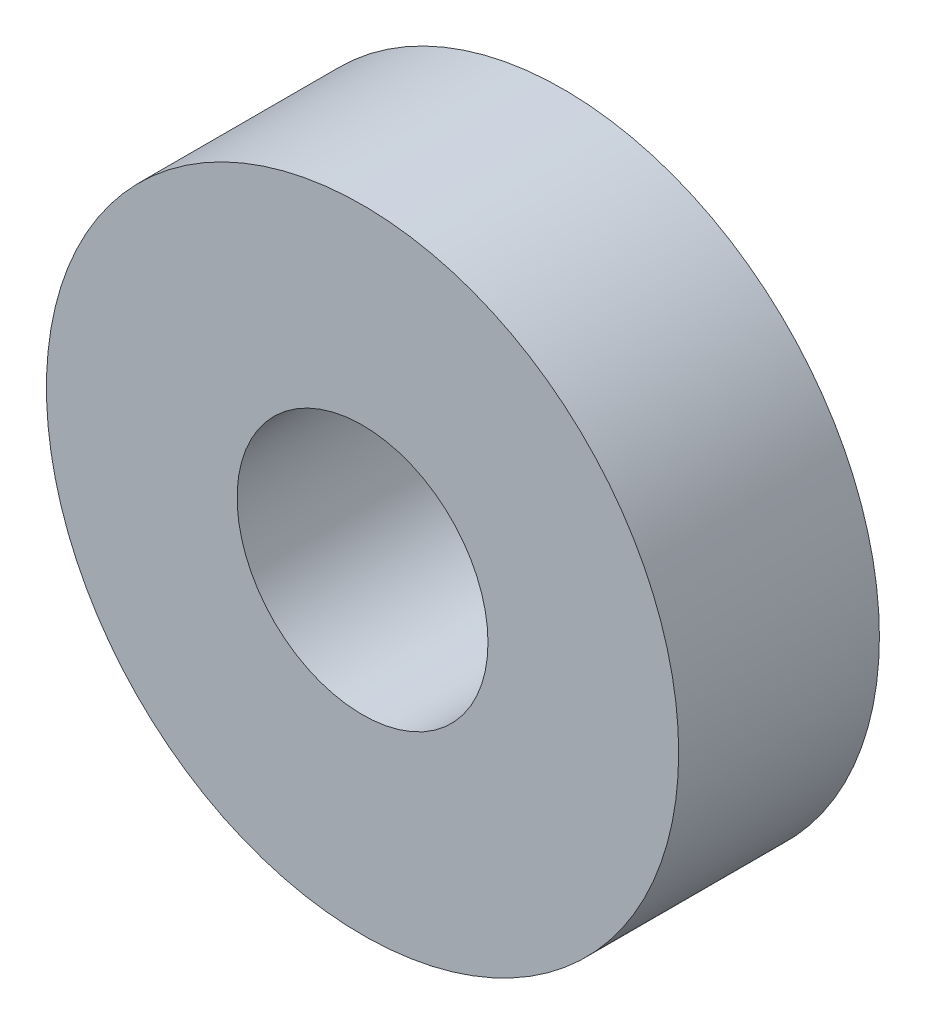
SolidWorks part; units mm, degrees
ref_plane "Plan de face" through (0, 0, 0) normal (0, 0, 1) x (1, 0, 0)
ref_plane "Plan de dessus" through (0, 0, 0) normal (0, 1, 0) x (1, 0, 0)
ref_plane "Plan de droite" through (0, 0, 0) normal (1, 0, 0) x (0, 0, -1)
sketch "Esquisse1" plane through (0, 0, 0) normal (0, 0, 1) x (1, 0, 0)
  circle A0 centre (0, 0) radius 15.75
  circle A1 centre (0, 0) radius 6.25
  dimension "D1" = 31.5
  dimension "D2" = 12.5
extrude "Boss.-Extru.1" add sketch "Esquisse1" along normal blind 10
